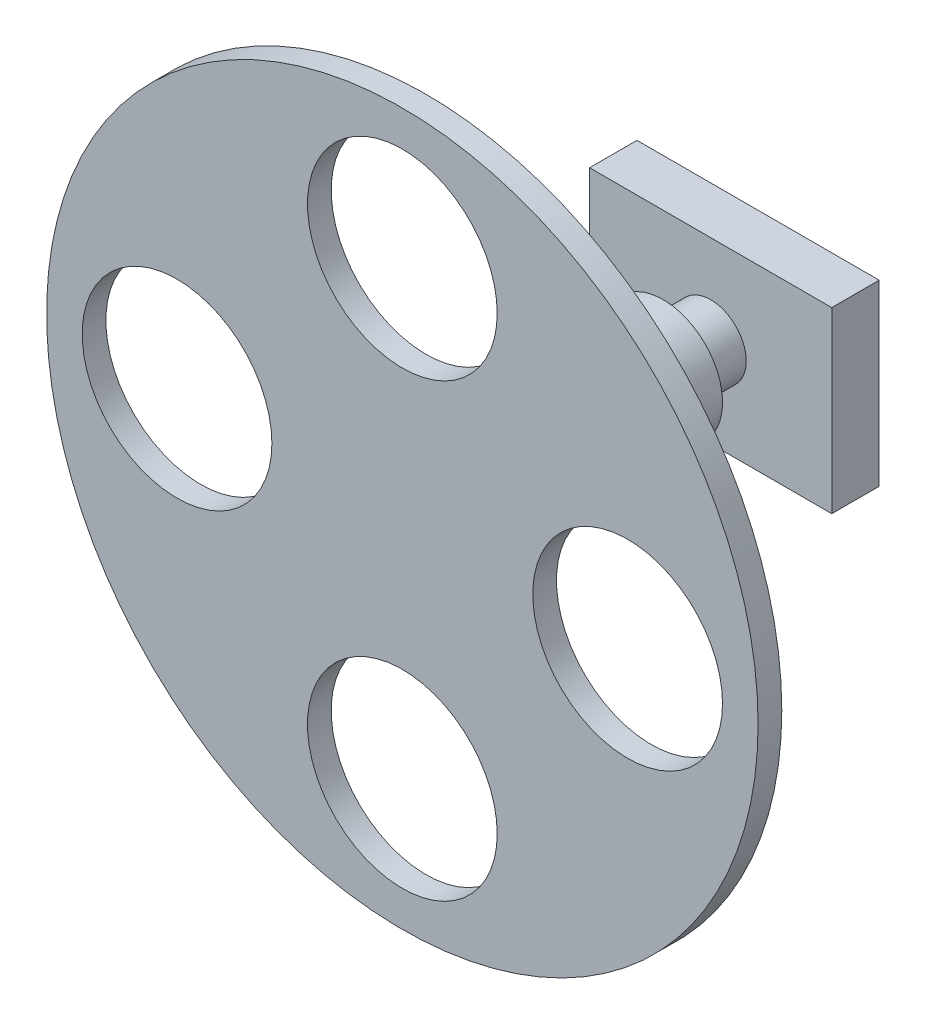
SolidWorks part; units mm, degrees
ref_plane "Front Plane" through (0, 0, 0) normal (0, 0, 1) x (1, 0, 0)
ref_plane "Top Plane" through (0, 0, 0) normal (0, 1, 0) x (1, 0, 0)
ref_plane "Right Plane" through (0, 0, 0) normal (1, 0, 0) x (0, 0, -1)
sketch "Sketch1" plane through (0, 0, 0) normal (0, 0, 1) x (1, 0, 0)
  circle A0 centre (0, 0) radius 150
  circle A1 centre (0, 95) radius 40
  circle A2 centre (95, 0) radius 40
  circle A3 centre (0, -95) radius 40
  circle A4 centre (-95, 0) radius 40
  point P14 (0, 0)
  dimension "D1" = 300
  dimension "D2" = 80
  dimension "D3" = 95
  dimension "D4" = 4
extrude "Boss-Extrude1" add sketch "Sketch1" along normal blind 10
sketch "Sketch2" plane through (0, 0, 0) normal (0, 0, -1) x (-1, 0, 0)
  circle A0 centre (0, 0) radius 25
  dimension "D1" = 50
extrude "Boss-Extrude2" add sketch "Sketch2" along normal blind 100
sketch "Sketch3" plane through (0, 0, -100) normal (0, 0, -1) x (-1, 0, 0)
  circle A0 centre (0, 0) radius 15
  dimension "D1" = 30
extrude "Boss-Extrude3" add sketch "Sketch3" along normal blind 20
sketch "Sketch4" plane through (0, 0, -120) normal (0, 0, -1) x (-1, 0, 0)
  line L1 (51.0627, -37.6363) -> (-51.0627, -37.6363)
  line L2 (51.0627, -37.6363) -> (51.0627, 37.6363)
  line L3 (51.0627, 37.6363) -> (-51.0627, 37.6363)
  line L4 (-51.0627, -37.6363) -> (-51.0627, 37.6363)
  line L5 (51.0627, -37.6363) -> (-51.0627, 37.6363) construction
  line L6 (51.0627, 37.6363) -> (-51.0627, -37.6363) construction
  point P0 (0, 0)
extrude "Boss-Extrude4" add sketch "Sketch4" along normal blind 20
